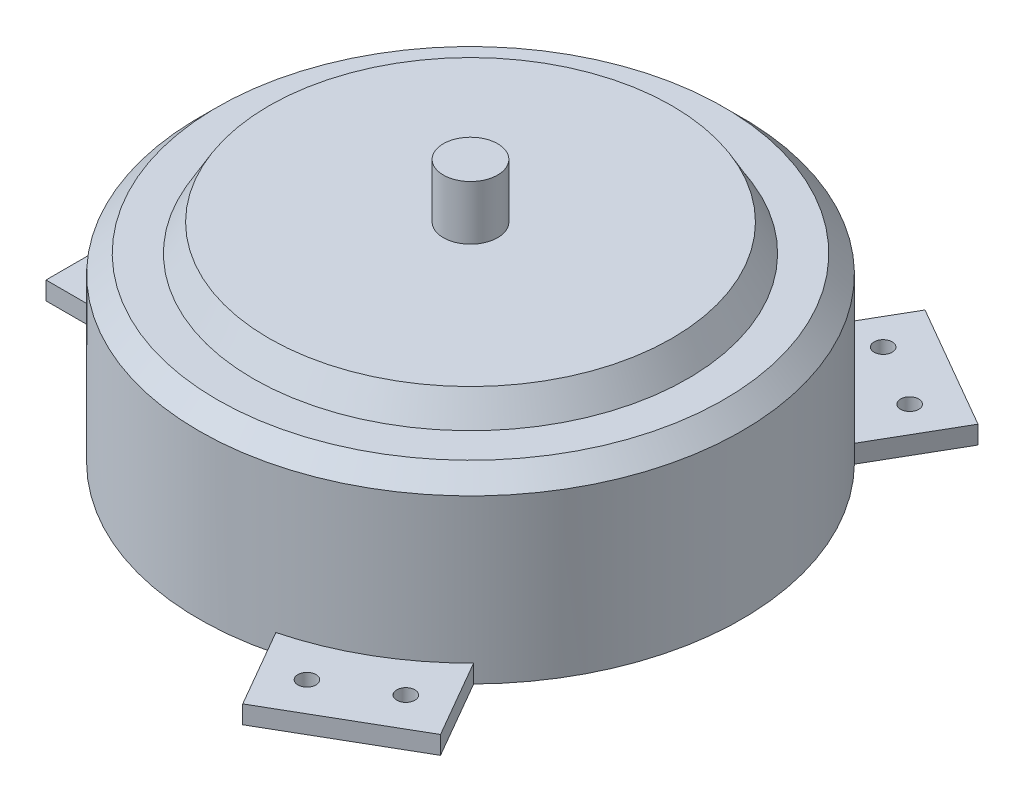
SolidWorks part; units mm, degrees
ref_plane "Front Plane" through (0, 0, 0) normal (0, 0, 1) x (1, 0, 0)
ref_plane "Top Plane" through (0, 0, 0) normal (0, 1, 0) x (1, 0, 0)
ref_plane "Right Plane" through (0, 0, 0) normal (1, 0, 0) x (0, 0, -1)
sketch "Sketch1" plane through (0, 0, 0) normal (0, 1, 0) x (1, 0, 0)
  circle A0 centre (0, 0) radius 150
  dimension "D1" = 300
extrude "Boss-Extrude1" add sketch "Sketch1" along normal blind 100
chamfer "Chamfer1" distance 10 angle 45 1 edges at (0, 100, 150)
sketch "Sketch2" plane through (0, 100, 0) normal (0, 1, 0) x (1, 0, 0)
  line L0 (-150, 0) -> (-194.5683, 0) construction
  line L1 (-194.5683, -40) -> (-194.5683, 40)
  line L2 (-144.5683, 40) -> (-194.5683, 40)
  line L3 (-194.5683, -40) -> (-144.5683, -40)
  circle A0 centre (0, 0) radius 150 construction
  arc A1 (-144.5683, 40) -> (-144.5683, -40) centre (0, 0) ccw
  point P6 (-194.5683, 0)
  dimension "D1" = 50
  dimension "D2" = 80
extrude "Boss-Extrude2" add sketch "Sketch2" along normal blind 10 from offset 100 contours A1 L3 L1 L2 offset against normal yes
sketch "Sketch3" plane through (0, 10, 0) normal (0, 1, 0) x (1, 0, 0)
  line L0 (-150, 0) -> (-194.5683, 0) construction
  line L1 (-194.5683, -40) -> (-194.5683, 40) construction
  line L2 (-172.2842, 0) -> (-172.2842, -40) construction
  line L3 (-194.5683, -40) -> (-144.5683, -40) construction
  line L4 (-172.2842, -40) -> (-172.2842, 0) construction
  line L6 (-172.2842, 0) -> (-172.2842, 40) construction
  line L7 (-144.5683, 40) -> (-194.5683, 40) construction
  arc A0 (-144.5683, 40) -> (-144.5683, -40) centre (0, 0) ccw construction
  circle A1 centre (-172.2842, -20) radius 5
  circle A2 centre (-172.2842, 20) radius 5
  dimension "D1" = 10
extrude "Cut-Extrude1" cut sketch "Sketch3" against normal blind 10
pattern_circular "CirPattern2" count 3 over 360 about axis through (0, 0, 0) along (0, 1, 0) of "Cut-Extrude1", "Boss-Extrude2"
sketch "Sketch4" plane through (0, 100, 0) normal (0, 1, 0) x (1, 0, 0)
  circle A2 centre (0, 0) radius 120
  circle A3 centre (0, 0) radius 120
  dimension "D1" = 20
extrude "Boss-Extrude4" add sketch "Sketch4" along normal blind 15 draft 30
sketch "Sketch5" plane through (0, 115, 0) normal (0, 1, 0) x (1, 0, 0)
  circle A0 centre (0, 0) radius 15
  dimension "D1" = 30
extrude "Boss-Extrude5" add sketch "Sketch5" along normal blind 30
